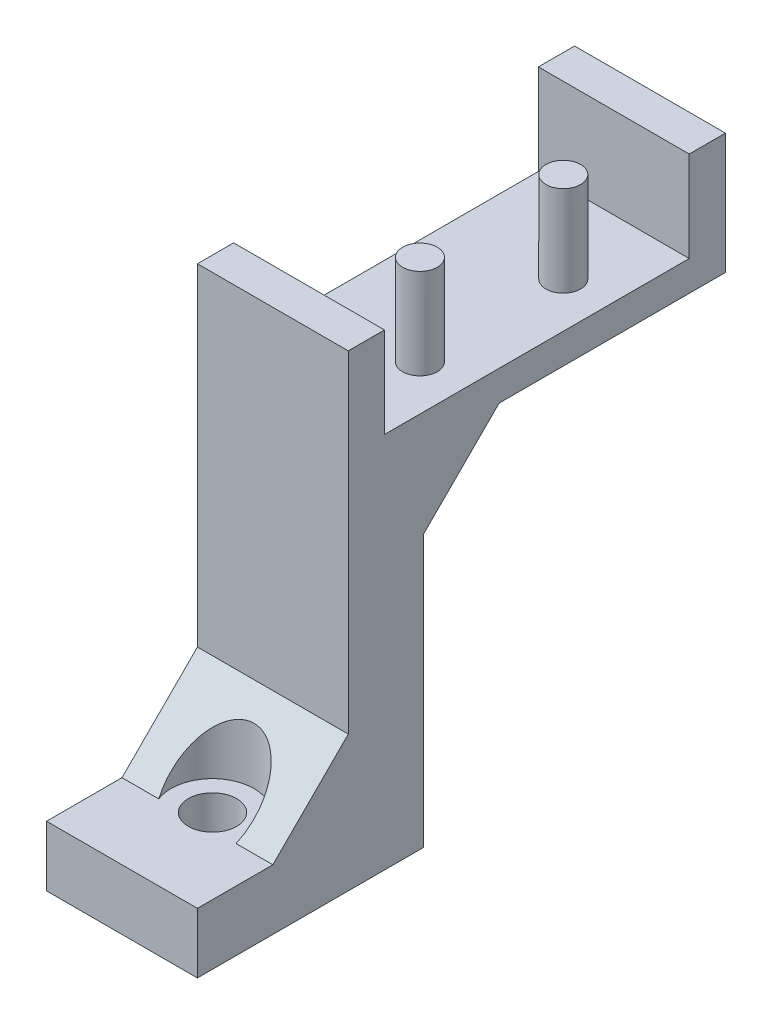
SolidWorks part; units mm, degrees
ref_plane "前视基准面" through (0, 0, 0) normal (0, 0, 1) x (1, 0, 0)
ref_plane "上视基准面" through (0, 0, 0) normal (0, 1, 0) x (1, 0, 0)
ref_plane "右视基准面" through (0, 0, 0) normal (1, 0, 0) x (0, 0, -1)
sketch "草图1" plane through (0, 0, 0) normal (1, 0, 0) x (0, 0, -1)
  line L0 (0, 0) -> (15, 0)
  line L1 (15, 0) -> (15, 23)
  line L2 (15, 23) -> (35, 23)
  line L3 (35, 23) -> (35, 31)
  line L4 (35, 31) -> (10, 31)
  line L5 (10, 31) -> (10, 4)
  line L6 (10, 4) -> (0, 4)
  line L7 (0, 4) -> (0, 0)
  dimension "D1" = 4
  dimension "D2" = 15
  dimension "D3" = 8
  dimension "D4" = 5
  dimension "D5" = 23
  dimension "D6" = 25
extrude "凸台-拉伸1" add sketch "草图1" along normal mid plane 10
sketch "草图2" plane through (0, 31, 0) normal (0, 1, 0) x (1, 0, 0)
  line L0 (-5, 32.6) -> (15, 32.6)
  line L1 (-5, 35) -> (-5, 10) construction
  line L2 (15, 32.6) -> (15, 12.4)
  line L3 (15, 12.4) -> (-5, 12.4)
  line L4 (-5, 12.4) -> (-5, 32.6)
  line L5 (5, 35) -> (-5, 35) construction
  dimension "D1" = 20.2
  dimension "D2" = 2.4
  dimension "D3" = 20
extrude "切除-拉伸1" cut sketch "草图2" against normal blind 6
sketch "草图3" plane through (0, 25, 0) normal (0, 1, 0) x (1, 0, 0)
  line L0 (5, 12.4) -> (5, 32.6) construction
  line L1 (2, 27.25) -> (2, 17.75) construction
  line L2 (2, 22.5) -> (5, 22.5) construction
  circle A0 centre (2, 27.25) radius 1.15
  circle A1 centre (2, 17.75) radius 1.15
  dimension "D1" = 2.3
  dimension "D2" = 2.3
  dimension "D3" = 3
  dimension "D4" = 3
  dimension "D5" = 9.5
extrude "凸台-拉伸2" add sketch "草图3" along normal blind 6
chamfer "倒角1" distance 5 angle 45 2 edges at (0, 4, -10) (0, 23, -15)
sketch "草图4" plane through (0, 0, 0) normal (0, -1, 0) x (1, 0, 0)
  line L0 (5, 0) -> (-5, 0) construction
  circle A0 centre (0, -6) radius 1.6
  dimension "D1" = 3.2
  dimension "D2" = 6
extrude "切除-拉伸2" cut sketch "草图4" against normal through all
sketch "草图5" plane through (0, 4, 0) normal (0, 1, 0) x (1, 0, 0)
  circle A0 centre (0, 6) radius 2.75
  dimension "D1" = 5.5
extrude "切除-拉伸3" cut sketch "草图5" along normal blind 6
